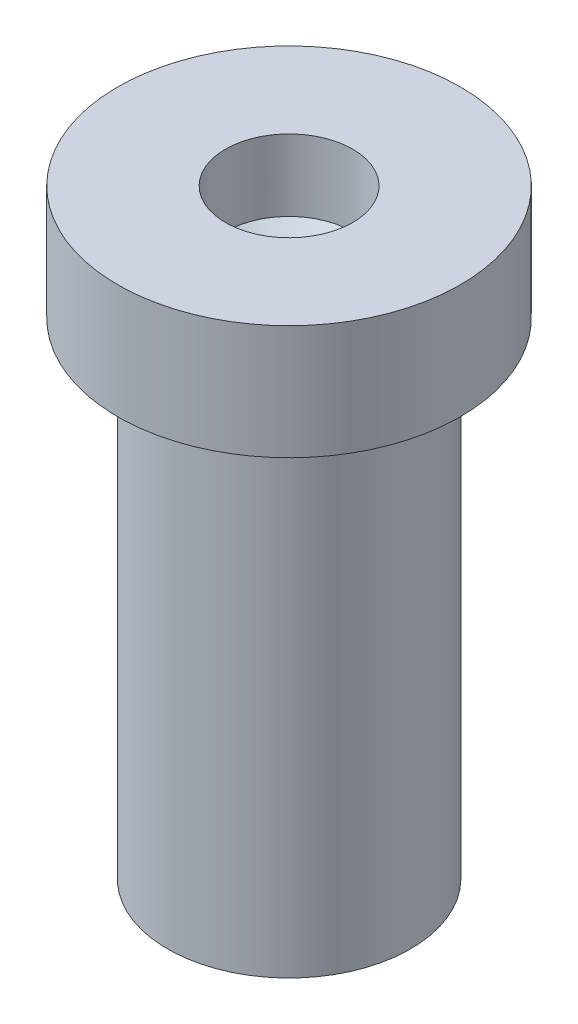
SolidWorks part; units mm, degrees
ref_plane "Front Plane" through (0, 0, 0) normal (0, 0, 1) x (1, 0, 0)
ref_plane "Top Plane" through (0, 0, 0) normal (0, 1, 0) x (1, 0, 0)
ref_plane "Right Plane" through (0, 0, 0) normal (1, 0, 0) x (0, 0, -1)
sketch "Sketch2" plane through (0, 0, 0) normal (0, 0, 1) x (1, 0, 0)
  line L0 (0, 0) -> (0, 10.1414) construction
  line L1 (0, 0) -> (1.75, 0)
  line L2 (1.75, 0) -> (1.75, 7)
  line L3 (1.75, 7) -> (2.4687, 7)
  line L4 (2.4687, 7) -> (2.4687, 8.6476)
  line L5 (2.4687, 8.6476) -> (0.9166, 8.6476)
  line L6 (0.9166, 8.6476) -> (0.9166, 7.6175)
  line L7 (0.9166, 7.6175) -> (0, 7)
  line L8 (0, 0) -> (0, 7)
  point P10 (0.8552, 7.3828)
  point P11 (0, 6.7263)
  point P12 (0.9166, 7.6175)
  point P13 (0, 7)
  dimension "D1" = 3.5
  dimension "D2" = 7
revolve "Revolve1" add sketch "Sketch2" angle 360 about L0
